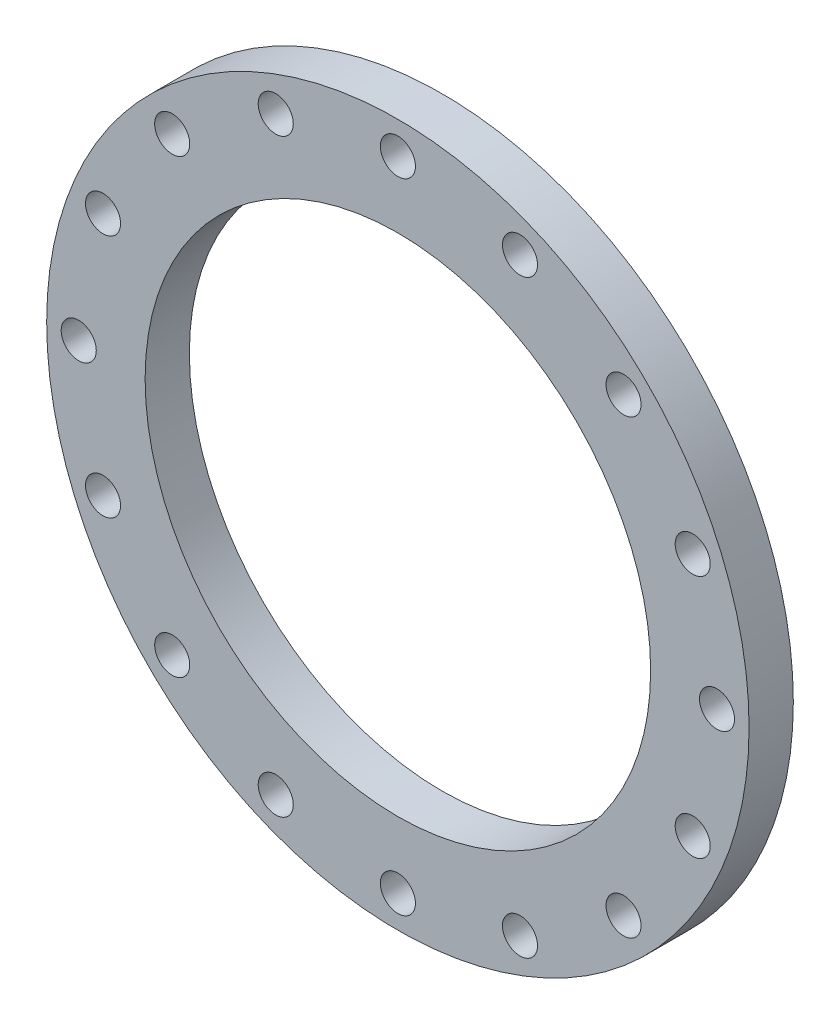
SolidWorks part; units mm, degrees
material "Alloy Steel"
ref_plane "Front Plane" through (0, 0, 0) normal (0, 0, 1) x (1, 0, 0)
ref_plane "Top Plane" through (0, 0, 0) normal (0, 1, 0) x (1, 0, 0)
ref_plane "Right Plane" through (0, 0, 0) normal (1, 0, 0) x (0, 0, -1)
sketch "Sketch11" plane through (0, 0, 0) normal (0, 0, 1) x (1, 0, 0)
  line L0 (0, 0) -> (0, -14778.7691) construction
  line L1 (0, 0) -> (-14778.7691, 0) construction
  circle A1 centre (0, 0) radius 228.5
  circle A2 centre (0, 0) radius 317.5
  circle A3 centre (0, 0) radius 288.5 construction
  circle A4 centre (0, 288.5) radius 15.85
  circle A5 centre (110.4042, 266.5392) radius 15.85
  circle A6 centre (204.0003, 204.0003) radius 15.85
  circle A7 centre (266.5392, 110.4042) radius 15.85
  circle A8 centre (288.5, 0) radius 15.85
  circle A9 centre (266.5392, -110.4042) radius 15.85
  circle A10 centre (204.0003, -204.0003) radius 15.85
  circle A11 centre (110.4042, -266.5392) radius 15.85
  circle A12 centre (0, -288.5) radius 15.85
  circle A13 centre (-110.4042, -266.5392) radius 15.85
  circle A14 centre (-204.0003, -204.0003) radius 15.85
  circle A15 centre (-266.5392, -110.4042) radius 15.85
  circle A16 centre (-288.5, 0) radius 15.85
  circle A17 centre (-266.5392, 110.4042) radius 15.85
  circle A18 centre (-204.0003, 204.0003) radius 15.85
  circle A19 centre (-110.4042, 266.5392) radius 15.85
  point P43 (0, 0)
  dimension "D1" = 457
  dimension "D2" = 635
  dimension "D3" = 577
  dimension "D4" = 31.7
  dimension "D5" = 16
extrude "Boss-Extrude1" add sketch "Sketch11" along normal blind 40
